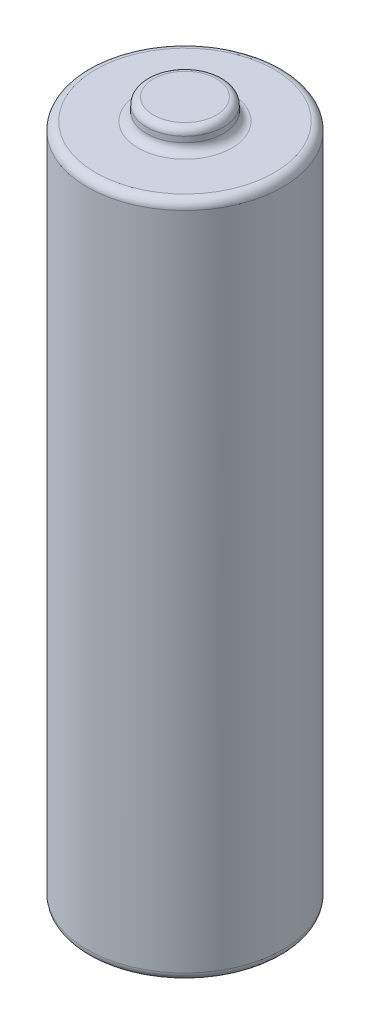
SolidWorks part; units mm, degrees
ref_plane "Front Plane" through (0, 0, 0) normal (0, 0, 1) x (1, 0, 0)
ref_plane "Top Plane" through (0, 0, 0) normal (0, 1, 0) x (1, 0, 0)
ref_plane "Right Plane" through (0, 0, 0) normal (1, 0, 0) x (0, 0, -1)
sketch "Sketch1" plane through (0, 0, 0) normal (0, 1, 0) x (1, 0, 0)
  circle A0 centre (0, 0) radius 7
  dimension "D1" = 14
extrude "Boss-Extrude1" add sketch "Sketch1" along normal blind 49
sketch "Sketch2" plane through (0, 49, 0) normal (0, 1, 0) x (1, 0, 0)
  circle A0 centre (0, 0) radius 2.75
  dimension "D1" = 5.5
extrude "Boss-Extrude2" add sketch "Sketch2" along normal blind 1.5
fillet "Fillet2" radius 0.6 1 edges at (0, 49, 2.75)
fillet "Fillet3" radius 0.5 1 edges at (0, 50.5, 2.75)
sketch "Sketch4" plane through (0, 0, 0) normal (0, -1, 0) x (1, 0, 0)
  circle A0 centre (0, 0) radius 4.6
  circle A1 centre (0, 0) radius 7
  dimension "D1" = 9.2
extrude "Cut-Extrude2" cut sketch "Sketch4" against normal blind 0.5
fillet "Fillet7" radius 0.6 1 edges at (0, 0.5, -7)
fillet "Fillet8" radius 0.6 1 edges at (0, 49, 7)
fillet "Fillet9" radius 0.1 1 edges at (0, 0, -4.6)
fillet "Fillet10" radius 0.5 1 edges at (0, 0.5, -4.6)
